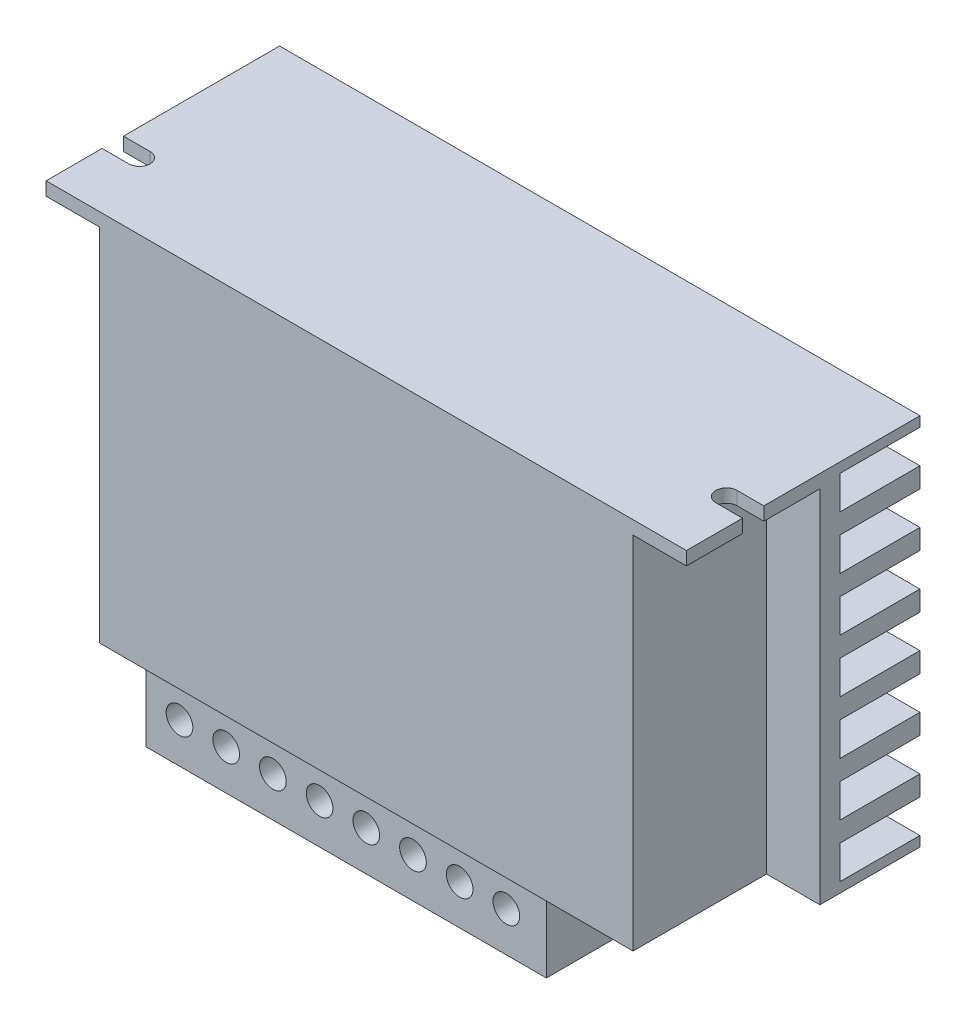
SolidWorks part; units mm, degrees
material "Простая углеродистая сталь"
ref_plane "Спереди" through (0, 0, 0) normal (0, 0, 1) x (1, 0, 0)
ref_plane "Сверху" through (0, 0, 0) normal (0, 1, 0) x (1, 0, 0)
ref_plane "Справа" through (0, 0, 0) normal (1, 0, 0) x (0, 0, -1)
sketch "Эскиз1" plane through (0, 0, 0) normal (0, 0, 1) x (1, 0, 0)
  line L0 (0, 0) -> (96, 0)
  line L1 (0, 0) -> (0, 56)
  line L2 (96, 0) -> (96, 56)
  line L3 (0, 56) -> (96, 56)
  dimension "D1" = 56
  dimension "D2" = 96
extrude "Бобышка-Вытянуть1" add sketch "Эскиз1" along normal blind 35
sketch "Эскиз5" plane through (96, 0, 0) normal (1, 0, 0) x (0, 0, -1)
  line L0 (-35, 54) -> (-15, 54)
  line L1 (-15, 54) -> (-15, 0)
  line L2 (-35, 56) -> (0, 56) construction
  line L3 (0, 0) -> (0, 56) construction
  line L4 (0, 0) -> (0, 56)
  line L5 (0, 56) -> (-35, 56)
  line L6 (-35, 56) -> (-35, 0)
  line L7 (-35, 0) -> (0, 0)
  line L10 (-35, 54) -> (-35, 0)
  line L11 (-35, 0) -> (-15, 0)
  dimension "D2" = 2
  dimension "D3" = 15
  dimension "D1" = 0
extrude "Вырез-Вытянуть3" cut sketch "Эскиз5" against normal blind 8
sketch "Эскиз6" plane through (0, 0, 0) normal (-1, 0, 0) x (0, 0, 1)
  line L4 (35, 0) -> (35, 54)
  line L5 (15, 0) -> (35, 0)
  line L6 (15, 54) -> (15, 0)
  line L7 (35, 54) -> (15, 54)
  line L8 (35, 0) -> (35, 54)
  line L9 (15, 0) -> (35, 0)
  line L10 (15, 54) -> (15, 0)
  line L11 (35, 54) -> (15, 54)
  dimension "D1" = 0
extrude "Вырез-Вытянуть4" cut sketch "Эскиз6" against normal blind 8
sketch "Эскиз7" plane through (96, 0, 0) normal (1, 0, 0) x (0, 0, -1)
  line L0 (-12, 1.5) -> (-12, 6.5)
  line L1 (-12, 1.5) -> (0, 1.5)
  line L2 (-12, 6.5) -> (0, 6.5)
  line L3 (0, 1.5) -> (0, 6.5)
  line L4 (0, 0) -> (0, 56) construction
  line L5 (-15, 0) -> (0, 0) construction
  line L6 (0, 9.5) -> (0, 14.5)
  line L7 (-12, 14.5) -> (0, 14.5)
  line L8 (-12, 9.5) -> (-12, 14.5)
  line L9 (-12, 9.5) -> (0, 9.5)
  line L10 (0, 17.5) -> (0, 22.5)
  line L11 (-12, 22.5) -> (0, 22.5)
  line L12 (-12, 17.5) -> (-12, 22.5)
  line L13 (-12, 17.5) -> (0, 17.5)
  line L14 (0, 25.5) -> (0, 30.5)
  line L15 (-12, 30.5) -> (0, 30.5)
  line L16 (-12, 25.5) -> (-12, 30.5)
  line L17 (-12, 25.5) -> (0, 25.5)
  line L18 (0, 33.5) -> (0, 38.5)
  line L19 (-12, 38.5) -> (0, 38.5)
  line L20 (-12, 33.5) -> (-12, 38.5)
  line L21 (-12, 33.5) -> (0, 33.5)
  line L22 (0, 41.5) -> (0, 46.5)
  line L23 (-12, 46.5) -> (0, 46.5)
  line L24 (-12, 41.5) -> (-12, 46.5)
  line L25 (-12, 41.5) -> (0, 41.5)
  line L26 (0, 49.5) -> (0, 54.5)
  line L27 (-12, 54.5) -> (0, 54.5)
  line L28 (-12, 49.5) -> (-12, 54.5)
  line L29 (-12, 49.5) -> (0, 49.5)
  line L30 (-35, 56) -> (0, 56) construction
  point P4 (-7.5, 0)
  dimension "D1" = 1.5
  dimension "D2" = 5
  dimension "D3" = 12
  dimension "D5" = 8
  dimension "D6" = 1.5
  dimension "D4" = 7
extrude "Вырез-Вытянуть5" cut sketch "Эскиз7" against normal through all
sketch "Эскиз8" plane through (0, 54, 0) normal (0, -1, 0) x (1, 0, 0)
  line L0 (88, 25) -> (96, 25) construction
  line L1 (88, 15) -> (88, 35) construction
  line L2 (96, 15) -> (96, 35) construction
  line L3 (92, 26.6) -> (96, 26.6)
  line L4 (96, 26.6) -> (96, 23.4)
  line L5 (96, 23.4) -> (92, 23.4)
  line L6 (96, 35) -> (0, 35) construction
  line L7 (48, 35) -> (48, 19.7888) construction
  line L8 (96, 26.6) -> (92, 26.6)
  line L9 (92, 23.4) -> (96, 23.4)
  line L10 (8, 25) -> (0, 25) construction
  line L11 (4, 23.4) -> (0, 23.4)
  line L12 (0, 26.6) -> (4, 26.6)
  line L13 (0, 23.4) -> (4, 23.4)
  line L14 (0, 26.6) -> (0, 23.4)
  line L15 (4, 26.6) -> (0, 26.6)
  arc A0 (92, 26.6) -> (92, 23.4) centre (92, 25) ccw
  arc A1 (4, 26.6) -> (4, 23.4) centre (4, 25) cw
  line M1 (96, 15) -> (96, 35)
  dimension "D1" = 3.2
extrude "Вырез-Вытянуть7" cut sketch "Эскиз8" against normal through all contours A1 L12 L14 L11 | L3 A0 L5 M1
sketch "Эскиз9" plane through (0, 0, 0) normal (0, -1, 0) x (1, 0, 0)
  line L0 (13, 33) -> (73, 33)
  line L1 (13, 33) -> (13, 18)
  line L2 (73, 33) -> (73, 18)
  line L3 (13, 18) -> (73, 18)
  line L4 (8, 35) -> (88, 35) construction
  line L5 (8, 15) -> (8, 35) construction
  dimension "D1" = 2
  dimension "D2" = 5
  dimension "D3" = 60
  dimension "D4" = 15
extrude "Бобышка-Вытянуть2" add sketch "Эскиз9" along normal blind 12
sketch "Эскиз10" plane through (0, 0, 33) normal (0, 0, 1) x (1, 0, 0)
  line L0 (13, -6) -> (73, -6) construction
  line L1 (13, -12) -> (13, 0) construction
  line L2 (73, -12) -> (73, 0) construction
  line L3 (20, -6) -> (80, -6) construction
  line L4 (27, -6) -> (87, -6) construction
  line L5 (34, -6) -> (94, -6) construction
  line L6 (41, -6) -> (101, -6) construction
  line L7 (48, -6) -> (108, -6) construction
  line L8 (55, -6) -> (115, -6) construction
  line L9 (62, -6) -> (122, -6) construction
  circle A0 centre (18, -6) radius 2
  circle A1 centre (25, -6) radius 2
  circle A2 centre (32, -6) radius 2
  circle A3 centre (39, -6) radius 2
  circle A4 centre (46, -6) radius 2
  circle A5 centre (53, -6) radius 2
  circle A6 centre (60, -6) radius 2
  circle A7 centre (67, -6) radius 2
  dimension "D1" = 4
  dimension "D2" = 5
  dimension "D4" = 7
  dimension "D3" = 8
extrude "Вырез-Вытянуть8" cut sketch "Эскиз10" against normal blind 3
sketch "Эскиз11" plane through (0, 0, 0) normal (0, 0, -1) x (-1, 0, 0)
  line L0 (-23, 63) -> (-73, 63) construction
  line L1 (-23, 63) -> (-23, 13) construction
  line L2 (-73, 63) -> (-73, 13) construction
  line L3 (-23, 13) -> (-73, 13) construction
  circle A0 centre (-23, 63) radius 2.25 construction
  circle A1 centre (-23, 63) radius 2.25 construction
  circle A2 centre (-73, 63) radius 2.25 construction
  circle A3 centre (-73, 63) radius 2.25 construction
  circle A4 centre (-23, 13) radius 2.25
  circle A5 centre (-73, 13) radius 2.25
  dimension "D1" = 50
extrude "Вырез-Вытянуть9" cut sketch "Эскиз11" against normal blind 15
